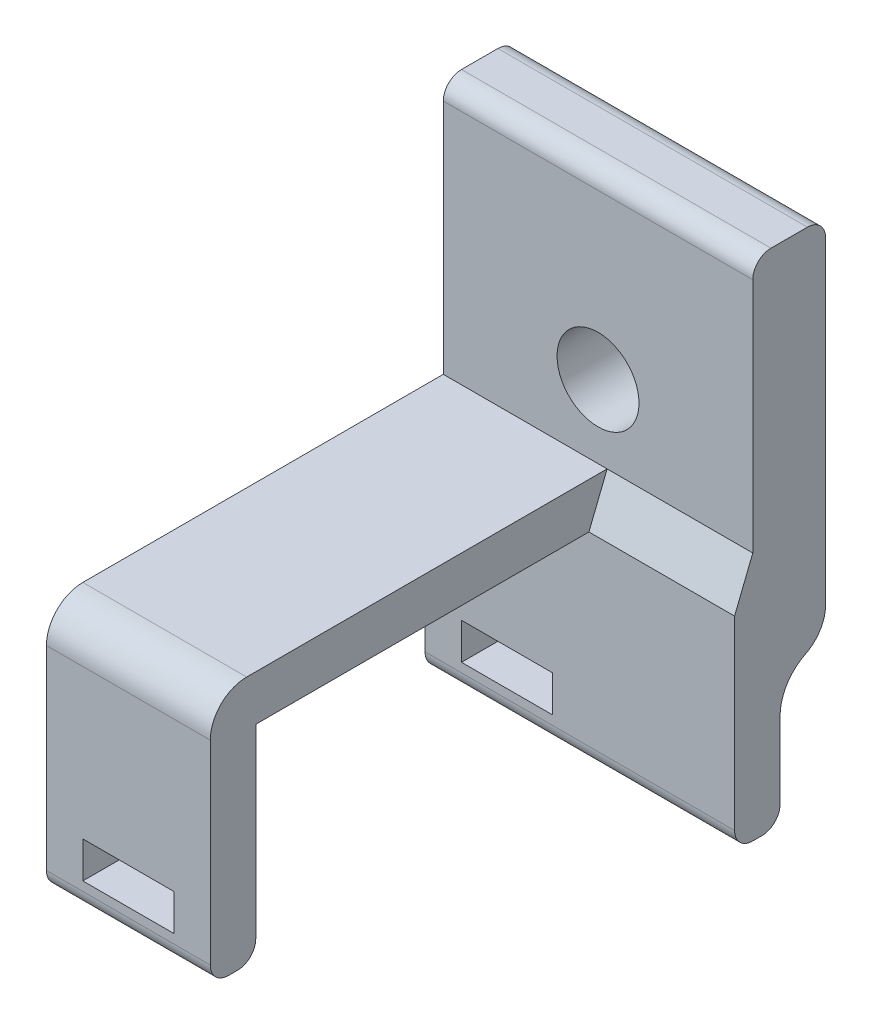
SolidWorks part; units mm, degrees
ref_plane "Front Plane" through (0, 0, 0) normal (0, 0, 1) x (1, 0, 0)
ref_plane "Top Plane" through (0, 0, 0) normal (0, 1, 0) x (1, 0, 0)
ref_plane "Right Plane" through (0, 0, 0) normal (1, 0, 0) x (0, 0, -1)
sketch "Sketch1" plane through (0, 0, 0) normal (0, 0, 1) x (1, 0, 0)
  line L1 (-40, -10) -> (40, -10) construction
  line L2 (-40, -10) -> (-40, 10) construction
  line L3 (-40, 10) -> (40, 10) construction
  line L4 (40, -10) -> (40, 10) construction
  line L5 (-40, -10) -> (40, 10) construction
  line L6 (-40, 10) -> (40, -10) construction
  line L7 (40, -3) -> (-40, -3) construction
  line L8 (40, -3) -> (40, 3) construction
  line L9 (40, 3) -> (-40, 3) construction
  line L10 (-40, -3) -> (-40, 3) construction
  line L11 (40, -3) -> (-40, 3) construction
  line L12 (40, 3) -> (-40, -3) construction
  point P0 (0, 0)
  point P6 (0, 0)
  dimension "D1" = 20
  dimension "D2" = 80
  dimension "D3" = 6
ref_plane "Plane1" through (0, 10, 0) normal (0, 1, 0) x (1, 0, 0)
sketch "Sketch2" plane through (0, 0, 0) normal (1, 0, 0) x (0, 0, -1)
  line L0 (-5, -6.5) -> (-23.3, -6.5)
  line L1 (-23.3, -6.5) -> (-23.3, -14.2)
  line L2 (-23.3, -14.2) -> (-5, -14.2)
  line L3 (-5, -14.2) -> (-5, -6.5)
  line L4 (-14.15, -6.5) -> (-14.15, -14.2) construction
  line L6 (0, -10) -> (0, 10) construction
  point P6 (-23.3, -11.6991)
  dimension "D1" = 18.3
  dimension "D2" = 7.7
  dimension "D5" = 3.5
  dimension "D6" = 5
sketch "Sketch3" plane through (0, 0, 0) normal (1, 0, 0) x (0, 0, -1)
  line L0 (-23.3, -14.2) -> (-23.3, -6.5)
  line L1 (-23.3, -6.5) -> (-5, -6.5)
  line L2 (-5, -6.5) -> (-5, -14.2)
  line L5 (0, -10) -> (0, 10)
  line L6 (-23.3, -6.5) -> (-23.3, -14.2) construction
  line L7 (-23.3, -14.2) -> (-25.8, -14.2)
  line L8 (-25.8, -14.2) -> (-25.8, -4)
  line L9 (-25.8, -4) -> (-4, -4)
  line L10 (-4, -4) -> (-4, 10)
  line L11 (-4, 10) -> (0, 10)
  line L12 (-5, -14.2) -> (-2.5, -14.2)
  line L14 (-2.5, -14.2) -> (-2.5, -12.5)
  line L15 (0, -10) -> (11.6623, -10) construction
  arc A0 (-2.5, -12.5) -> (0, -10) centre (0, -12.5) cw
  dimension "D1" = 2.5
  dimension "D2" = 2.5
  dimension "D3" = 2.5
  dimension "D4" = 4
extrude "Boss-Extrude1" add sketch "Sketch3" along normal mid plane 9 contours L9 L10 L11 L5 A0 L14 L12 L2 L1 L0 L7 L8
fillet "Fillet1" radius 2 2 edges at (0, -10, 0) (0, -4, 25.8)
sketch "Sketch8" plane through (4.5, 0, 0) normal (1, 0, 0) x (0, 0, -1)
  line L0 (-4, -4) -> (-5, -6.5)
  line L11 (0, -8.4689) -> (0, 10)
  line L12 (0, 10) -> (-4, 10)
  line L13 (-4, 10) -> (-4, -4)
  line L14 (-4, -4) -> (-23.8, -4)
  line L15 (-25.8, -6) -> (-25.8, -14.2)
  line L16 (-25.8, -14.2) -> (-23.3, -14.2)
  line L17 (-23.3, -14.2) -> (-23.3, -6.5)
  line L18 (-23.3, -6.5) -> (-5, -6.5)
  line L19 (-5, -6.5) -> (-5, -14.2)
  line L20 (-5, -14.2) -> (-2.5, -14.2)
  line L21 (-2.5, -14.2) -> (-2.5, -12.5)
  line L22 (0, -8.4689) -> (0, 10)
  line L23 (0, 10) -> (-4, 10)
  line L24 (-4, 10) -> (-4, -4)
  line L30 (-5, -6.5) -> (-5, -14.2)
  line L31 (-5, -14.2) -> (-2.5, -14.2)
  line L32 (-2.5, -14.2) -> (-2.5, -12.5)
  arc A9 (-23.8, -4) -> (-25.8, -6) centre (-23.8, -6) ccw
  arc A12 (-1.1111, -10.2605) -> (-2.5, -12.5) centre (0, -12.5) ccw
  arc A13 (-1.1111, -10.2605) -> (0, -8.4689) centre (-2, -8.4689) ccw
  arc A19 (-1.1111, -10.2605) -> (-2.5, -12.5) centre (0, -12.5) ccw
  arc A20 (-1.1111, -10.2605) -> (0, -8.4689) centre (-2, -8.4689) ccw
  dimension "D1" = 0
extrude "Boss-Extrude2" add sketch "Sketch8" along normal blind 8
hole_wizard "M4 Clearance Hole1" positions "Sketch4" profile "Sketch6" hole size "M4" standard "ISO"
sketch "Sketch4" plane through (0, 0, 0) normal (0, 0, 1) x (1, 0, 0)
  line L0 (-4.5, 0) -> (12.5, 0) construction
  line L2 (12.5, 10) -> (12.5, -4) construction
  line L3 (-4.5, -4) -> (-4.5, 10) construction
  point P0 (4, 0)
sketch "Sketch6" plane through (4, 0, 0) normal (1, 0, 0) x (0, 1, 0)
  line L0 (0, 0) -> (0, 13.7519)
  line L1 (0, 13.7519) -> (2.25, 12.4)
  line L2 (2.25, 12.4) -> (2.25, 0)
  line L5 (2.25, 0) -> (0, 0)
  line L10 (0, 13.7519) -> (-2.25, 12.4) construction
  line L11 (0, -6.35) -> (0, 107.95) construction
  dimension "Hole Dia." = 4.5
  dimension "Hole Depth" = 12.4
  dimension "Drill Angle" = 118
sketch "Sketch9" plane through (0, 0, 25.8) normal (0, 0, 1) x (1, 0, 0)
  line L1 (-4.5, -14.2) -> (4.5, -14.2)
  line L2 (-4.5, -14.2) -> (-4.5, -17.7)
  line L3 (-4.5, -17.7) -> (4.5, -17.7)
  line L4 (4.5, -14.2) -> (4.5, -17.7)
  line L5 (4.5, -14.2) -> (4.5, -6) construction
  dimension "D1" = 3.5
extrude "Boss-Extrude3" add sketch "Sketch9" against normal up to surface (2.5 mm away) up to face at (0, -10.35, 23.3)
sketch "Sketch10" plane through (0, 0, 5) normal (0, 0, 1) x (1, 0, 0)
  line L0 (12.5, -14.2) -> (-4.5, -14.2) construction
  line L1 (-4.5, -14.2) -> (12.5, -14.2)
  line L2 (-4.5, -14.2) -> (-4.5, -17.7)
  line L3 (-4.5, -17.7) -> (12.5, -17.7)
  line L4 (12.5, -14.2) -> (12.5, -17.7)
  line L5 (4.5, -17.7) -> (-4.5, -17.7) construction
extrude "Boss-Extrude4" add sketch "Sketch10" against normal up to surface (2.5 mm away) up to face at (4, -13.35, 2.5)
sketch "Sketch11" plane through (0, 0, 25.8) normal (0, 0, 1) x (1, 0, 0)
  line L0 (0, -6.5) -> (0, -14.2) construction
  line L1 (-2.5, -16.2) -> (2.5, -16.2)
  line L2 (-2.5, -16.2) -> (-2.5, -14.2)
  line L3 (-2.5, -14.2) -> (2.5, -14.2)
  line L4 (2.5, -16.2) -> (2.5, -14.2)
  line L5 (-2.5, -16.2) -> (2.5, -14.2) construction
  line L6 (-2.5, -14.2) -> (2.5, -16.2) construction
  point P0 (0, -15.2)
  dimension "D1" = 5
  dimension "D2" = 2
extrude "Cut-Extrude1" cut sketch "Sketch11" against normal through all
fillet "Fillet2" radius 1 6 edges at (4, 10, 0) (4, 10, 4) (4, -17.7, 2.5) (4, -17.7, 5) (0, -17.7, 23.3) (0, -17.7, 25.8)
